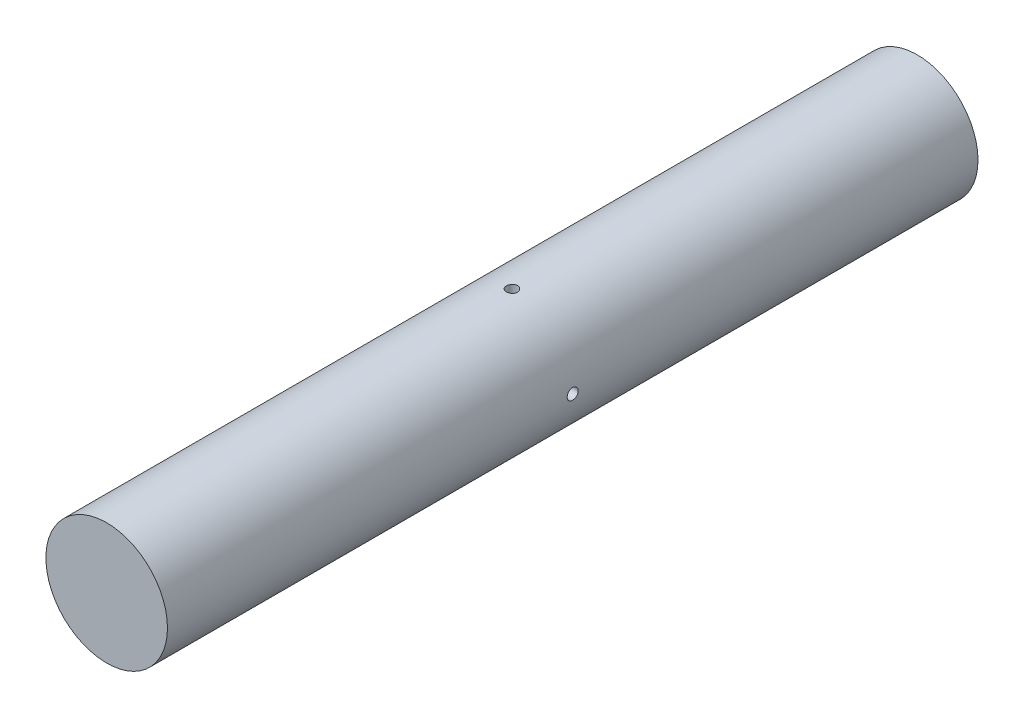
SolidWorks part; units mm, degrees
ref_plane "Front Plane" through (0, 0, 0) normal (0, 0, 1) x (1, 0, 0)
ref_plane "Top Plane" through (0, 0, 0) normal (0, 1, 0) x (1, 0, 0)
ref_plane "Right Plane" through (0, 0, 0) normal (1, 0, 0) x (0, 0, -1)
sketch "Sketch1" plane through (0, 0, 0) normal (0, 0, 1) x (1, 0, 0)
  circle A0 centre (0, 0) radius 37.5
  dimension "D1" = 75
extrude "Boss-Extrude1" add sketch "Sketch1" along normal mid plane 500
ref_plane "Plane1" through (0, 37.5, 0) normal (0, 1, 0) x (1, 0, 0)
ref_plane "Plane2" through (0, -37.5, 0) normal (0, -1, 0) x (-1, 0, 0)
ref_plane "Plane3" through (-37.5, 0, 0) normal (-1, 0, 0) x (0, 0, 1)
ref_plane "Plane4" through (37.5, 0, 0) normal (1, 0, 0) x (0, 0, -1)
hole_wizard "M8x1.25 Tapped Hole1" positions "Sketch6" profile "Sketch8" tap size "M8x1.25" standard "ANSI Metric"
sketch "Sketch6" plane through (0, -37.5, 0) normal (0, -1, 0) x (-1, 0, 0)
  point P0 (0, 0)
sketch "Sketch8" plane through (0, -37.5, 0) normal (1, 0, 0) x (0, 0, -1)
  line L0 (0, 0) -> (0, 23.2929)
  line L1 (0, 23.2929) -> (3.4, 21.25)
  line L2 (3.4, 21.25) -> (3.4, 0)
  line L5 (3.4, 0) -> (0, 0)
  line L10 (0, 23.2929) -> (-3.4, 21.25) construction
  line L11 (0, -6.35) -> (0, 107.95) construction
  dimension "Tap Drill Dia." = 6.8
  dimension "Tap Drill Depth" = 21.25
  dimension "Drill Angle" = 118
cosmetic thread "Hole Thread1" parameters "D1"=15, "D2"=8
hole_wizard "M8x1.25 Tapped Hole2" positions "Sketch9" profile "Sketch10" tap size "M8x1.25" standard "ANSI Metric"
sketch "Sketch9" plane through (0, 37.5, 0) normal (0, 1, 0) x (1, 0, 0)
  point P0 (0, 0)
sketch "Sketch10" plane through (0, 37.5, 0) normal (1, 0, 0) x (0, 0, 1)
  line L0 (0, 0) -> (0, 23.2929)
  line L1 (0, 23.2929) -> (3.4, 21.25)
  line L2 (3.4, 21.25) -> (3.4, 0)
  line L5 (3.4, 0) -> (0, 0)
  line L10 (0, 23.2929) -> (-3.4, 21.25) construction
  line L11 (0, -6.35) -> (0, 107.95) construction
  dimension "Tap Drill Dia." = 6.8
  dimension "Tap Drill Depth" = 21.25
  dimension "Drill Angle" = 118
cosmetic thread "Hole Thread2" parameters "D1"=15, "D2"=8
hole_wizard "M8x1.25 Tapped Hole3" positions "Sketch11" profile "Sketch12" tap size "M8x1.25" standard "ANSI Metric"
sketch "Sketch11" plane through (37.5, 0, 0) normal (1, 0, 0) x (0, 0, -1)
  point P0 (0, 0)
sketch "Sketch12" plane through (37.5, 0, 0) normal (0, 1, 0) x (0, 0, -1)
  line L0 (0, 0) -> (0, 23.2929)
  line L1 (0, 23.2929) -> (3.4, 21.25)
  line L2 (3.4, 21.25) -> (3.4, 0)
  line L5 (3.4, 0) -> (0, 0)
  line L10 (0, 23.2929) -> (-3.4, 21.25) construction
  line L11 (0, -6.35) -> (0, 107.95) construction
  dimension "Tap Drill Dia." = 6.8
  dimension "Tap Drill Depth" = 21.25
  dimension "Drill Angle" = 118
cosmetic thread "Hole Thread3" parameters "D1"=15, "D2"=8
hole_wizard "M8x1.25 Tapped Hole4" positions "Sketch13" profile "Sketch14" tap size "M8x1.25" standard "ANSI Metric"
sketch "Sketch13" plane through (-37.5, 0, 0) normal (-1, 0, 0) x (0, 0, 1)
  point P0 (0, 0)
sketch "Sketch14" plane through (-37.5, 0, 0) normal (0, 1, 0) x (0, 0, 1)
  line L0 (0, 0) -> (0, 23.2929)
  line L1 (0, 23.2929) -> (3.4, 21.25)
  line L2 (3.4, 21.25) -> (3.4, 0)
  line L5 (3.4, 0) -> (0, 0)
  line L10 (0, 23.2929) -> (-3.4, 21.25) construction
  line L11 (0, -6.35) -> (0, 107.95) construction
  dimension "Tap Drill Dia." = 6.8
  dimension "Tap Drill Depth" = 21.25
  dimension "Drill Angle" = 118
cosmetic thread "Hole Thread4" parameters "D1"=15, "D2"=8
